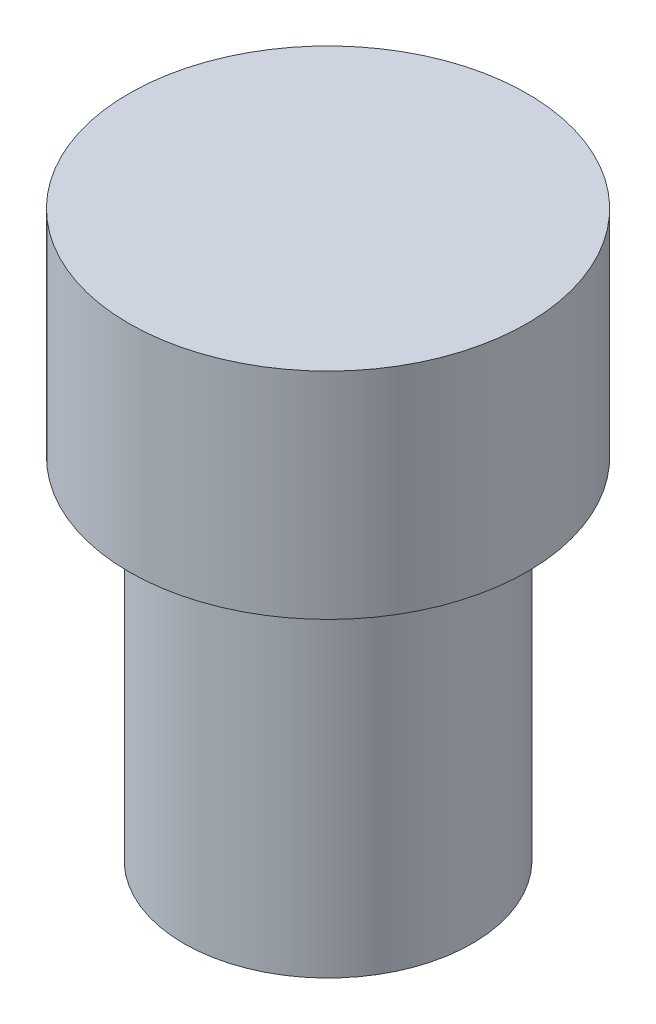
SolidWorks part; units mm, degrees
ref_plane "Front Plane" through (0, 0, 0) normal (0, 0, 1) x (1, 0, 0)
ref_plane "Top Plane" through (0, 0, 0) normal (0, 1, 0) x (1, 0, 0)
ref_plane "Right Plane" through (0, 0, 0) normal (1, 0, 0) x (0, 0, -1)
sketch "Sketch2" plane through (0, 0, 0) normal (0, 1, 0) x (1, 0, 0)
  circle A0 centre (0, 0) radius 32.1849
  point P2 (-33.5264, 9.9443)
extrude "Boss-Extrude1" add sketch "Sketch2" along normal blind 78 contours A0
sketch "Sketch3" plane through (0, 78, 0) normal (0, 1, 0) x (1, 0, 0)
  circle A0 centre (0, 0) radius 44.4528
  point P2 (0, 0)
  point P3 (0, 0)
extrude "Boss-Extrude2" add sketch "Sketch3" along normal blind 48
